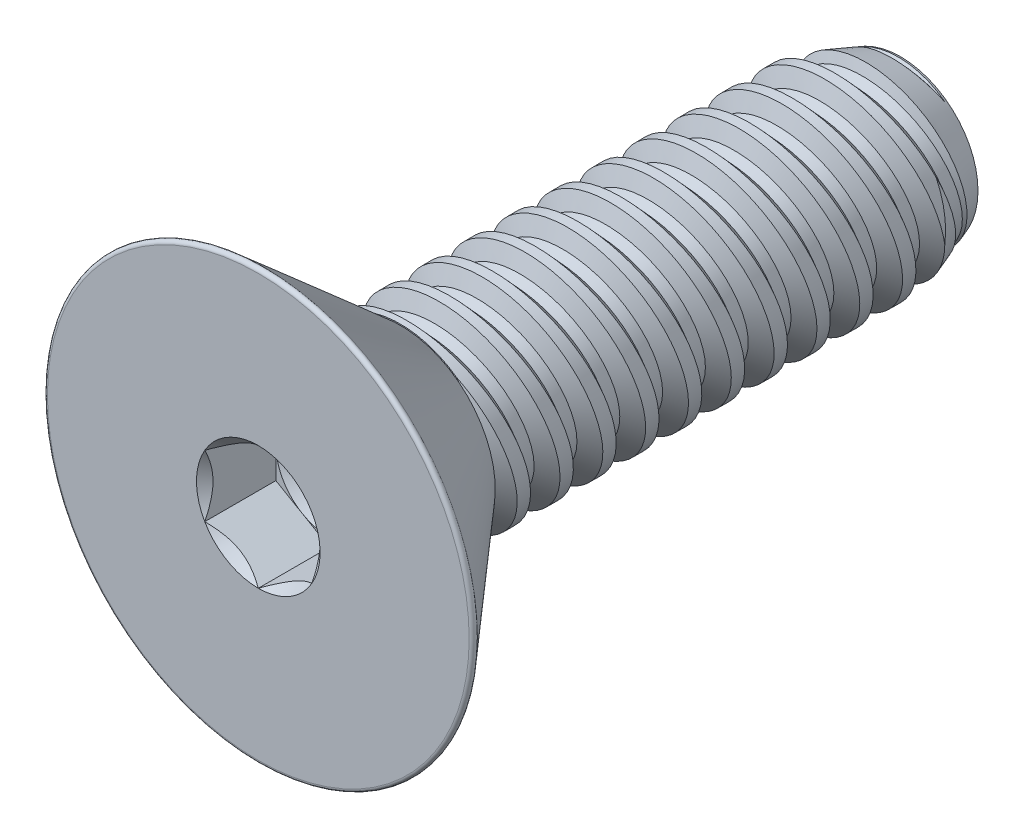
SolidWorks part; units mm, degrees
material "Alloy Steel"
ref_plane "Front" through (0, 0, 0) normal (0, 0, 1) x (1, 0, 0)
ref_plane "Top" through (0, 0, 0) normal (0, 1, 0) x (1, 0, 0)
ref_plane "Right" through (0, 0, 0) normal (1, 0, 0) x (0, 0, -1)
sketch "Sketch1" plane through (0, 0, 0) normal (1, 0, 0) x (0, 0, -1)
  line L0 (0, 0) -> (-2.1082, 0) construction
  line L1 (0, 0) -> (7.4168, 0)
  line L2 (0, 0) -> (0, 1.4224)
  line L3 (0, 1.4224) -> (7.4168, 1.4224)
  line L4 (7.4168, 0) -> (7.4168, 1.4224)
  line L5 (0, -1.4224) -> (7.4168, -1.4224) construction
  dimension "D1" = 7.4168
  dimension "Thread Dia" = 2.8448
  dimension "Length" = 9.525
  dimension "Head Height" = 2.1082
revolve "Revolve1" add sketch "Sketch1" angle 360 about L0
ref_plane "Plane1" through (0, 0, 2.1082) normal (0, 0, 1) x (1, 0, 0)
sketch "Sketch2" plane through (0, 0, 0) normal (1, 0, 0) x (0, 0, -1)
  line L0 (0, 1.4224) -> (0, -1.4224) construction
  line L1 (0, -1.4224) -> (0.635, -1.4224) construction
  line L2 (0.635, -1.4224) -> (0, 1.4224) construction
  line L3 (0, 1.4224) -> (0.0775, 1.4397) construction
  line L4 (0.0775, 1.4397) -> (0.6197, 1.5607)
  line L5 (0.6197, 1.5607) -> (0.501, 1.1821)
  line L6 (0.501, 1.1821) -> (0.346, 1.1475)
  line L7 (0.346, 1.1475) -> (0.0775, 1.4397)
  line L8 (0.4235, 1.1648) -> (0.3486, 1.5002) construction
  line L9 (0, -1.4224) -> (7.4168, -1.4224) construction
  line L10 (0, 1.4224) -> (7.4168, 1.4224) construction
  line L12 (0.366, 1.4224) -> (1.001, -1.4224) construction
  line L13 (0, -0.1526) -> (1.367, 0.1526) construction
  line L15 (0, 0) -> (0, 1.4224) construction
  point P19 (0.6835, 0)
  dimension "D1" = 60
  dimension "Thread Pitch" = 0.635
  dimension "D2" = 0.0794
  dimension "D3" = 0.1588
  dimension "D4" = 0.635
revolve "Cut-Revolve1" cut sketch "Sketch2" angle 360 about L13
sketch "Sketch3" plane through (0, 0, 0) normal (1, 0, 0) x (0, 0, -1)
  line L0 (7.4168, 1.1475) -> (6.6614, 1.4224)
  line L1 (6.6614, 1.4224) -> (7.4168, 1.4224)
  line L2 (7.4168, 1.4224) -> (7.4168, 1.1475)
  line L3 (0, 1.4224) -> (7.4168, 1.4224) construction
  line L4 (7.4168, 0) -> (7.4168, 1.4224) construction
  line L5 (6.6614, 0) -> (0, 0) construction
  line L6 (6.6614, 1.4224) -> (6.6614, -1.4224) construction
  line L7 (0, -1.4224) -> (7.4168, -1.4224) construction
  dimension "D1" = 20
  dimension "D2" = 2.8448
revolve "Cut-Revolve2" cut sketch "Sketch3" angle 360 about L5
pattern_linear "LPattern1" count 12 spacing 0.635 along (0, 0, 1)
pattern_linear "LPattern2" count 2 spacing 0.635 along (0, 0, 1)
sketch "Sketch4" plane through (0, 0, 0) normal (0, 0, 1) x (1, 0, 0)
  circle A0 centre (0, 0) radius 3.2385
  dimension "Head Dia" = 6.477
extrude "Extrude1" add sketch "Sketch4" along normal up to surface (2.1082 mm away)
sketch "Sketch9" plane through (0, 0, 0) normal (1, 0, 0) x (0, 0, -1)
  line L0 (-2.1082, 3.2385) -> (0, 1.4059)
  line L1 (0, 1.4059) -> (0, 3.2385)
  line L2 (0, 3.2385) -> (-2.1082, 3.2385)
  line L3 (0, 0) -> (-2.1082, 0) construction
  line L6 (-2.1082, -3.2385) -> (0, -1.4059) construction
  line L7 (0, -3.2385) -> (0, 3.2385) construction
  line L8 (-2.1082, 3.2385) -> (-2.1082, -3.2385) construction
  line L9 (0, 3.2385) -> (-2.1082, 3.2385) construction
  dimension "D1" = 82
revolve "Cut-Revolve3" cut sketch "Sketch9" angle 360 about L3
fillet "Fillet1" radius 0.0508
sketch "Sketch6" plane through (0, 0, 2.1082) normal (0, 0, 1) x (1, 0, 0)
  line L1 (0, -0.9165) -> (0.7937, -0.4583)
  line L2 (0.7937, -0.4583) -> (0.7937, 0.4583)
  line L3 (0.7937, 0.4583) -> (0, 0.9165)
  line L4 (0, 0.9165) -> (-0.7938, 0.4583)
  line L5 (-0.7938, 0.4583) -> (-0.7938, -0.4583)
  line L6 (-0.7938, -0.4583) -> (0, -0.9165)
  circle A0 centre (0, 0) radius 0.7938 construction
  dimension "Hex" = 1.5875
extrude "Cut-Extrude1" cut sketch "Sketch6" against normal blind 1.0541
sketch "Sketch7" plane through (0, 0, 2.1082) normal (0, 0, 1) x (1, 0, 0)
  circle A0 centre (0, 0) radius 0.9165
extrude "Cut-Extrude4" cut sketch "Sketch7" against normal blind 1.0541 draft 45
sketch "Sketch8" plane through (0, 0, 1.0541) normal (0, 0, 1) x (1, 0, 0)
  circle A0 centre (0, 0) radius 0.7938 construction
  circle A1 centre (0, 0) radius 0.7938
extrude "Cut-Extrude5" cut sketch "Sketch8" against normal blind 0.3514 draft 60
equation "\"D2@Sketch2\"=\"Thread Pitch@Sketch2\"/8"
equation "\"D3@Sketch2\"=\"Thread Pitch@Sketch2\"/4"
equation "\"D4@Sketch2\"=\"Thread Pitch@Sketch2\""
equation "\"D3@LPattern1\"=\"Thread Pitch@Sketch2\""
equation "\"D1@Cut-Extrude1\"=\"Head Height@Sketch1\"/2"
equation "\"D1@Cut-Extrude4\"=\"D1@Cut-Extrude1\""
equation "\"D1@Cut-Extrude5\"=\"D1@Cut-Extrude1\"/3"
equation "\"D1@LPattern1\"=\"D1@Sketch1\"/\"Thread Pitch@Sketch2\""
equation "\"D3@LPattern2\"=\"Thread Pitch@Sketch2\""
